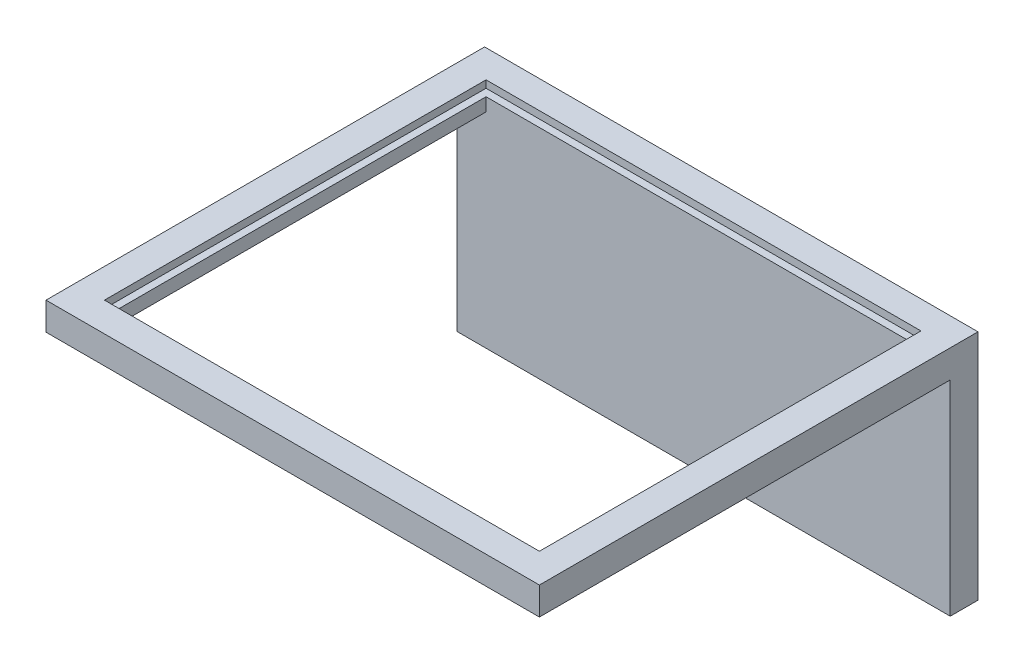
SolidWorks part; units mm, degrees
ref_plane "Plan de face" through (0, 0, 0) normal (0, 0, 1) x (1, 0, 0)
ref_plane "Plan de dessus" through (0, 0, 0) normal (0, 1, 0) x (1, 0, 0)
ref_plane "Plan de droite" through (0, 0, 0) normal (1, 0, 0) x (0, 0, -1)
sketch "Esquisse1" plane through (0, 0, 0) normal (0, 0, 1) x (1, 0, 0)
  line L1 (0, 0) -> (33.75, 0)
  line L2 (0, 0) -> (0, 14)
  line L3 (0, 14) -> (33.75, 14)
  line L4 (33.75, 0) -> (33.75, 14)
  point P4 (0, 0)
  dimension "D1" = 33.75
  dimension "D2" = 14
extrude "Boss.-Extru.1" add sketch "Esquisse1" along normal blind 1.9
sketch "Esquisse2" plane through (0, 14, 0) normal (0, 1, 0) x (1, 0, 0)
  line L0 (33.75, -1.9) -> (33.75, 0) construction
  line L1 (0, 0) -> (33.75, 0)
  line L2 (0, 0) -> (0, -30)
  line L3 (0, -30) -> (33.75, -30)
  line L4 (33.75, 0) -> (33.75, -30)
  line L5 (33.75, -1.9) -> (0, -1.9) construction
  line L6 (2, -1.9) -> (31.75, -1.9)
  line L7 (2, -1.9) -> (2, -28)
  line L8 (2, -28) -> (31.75, -28)
  line L9 (31.75, -1.9) -> (31.75, -28)
  point P11 (0, 0)
  point P12 (0, 0)
  point P13 (2, -1.9)
  line M9 (33.75, 0) -> (0, 0)
  line M10 (0, 0) -> (0, -1.9)
  line M11 (0, -1.9) -> (33.75, -1.9)
  line M12 (33.75, -1.9) -> (33.75, 0)
  dimension "D1" = 30
  dimension "D2" = 2
  dimension "D3" = 2
  dimension "D4" = 2
extrude "Boss.-Extru.2" add sketch "Esquisse2" along normal blind 1.9 contours L9 L8 L7 L2 L3 L4 M11 | L7 M9 M10 M11 | L9 M9 M11 M12
sketch "Esquisse4" plane through (0, 15.9, 0) normal (0, 1, 0) x (1, 0, 0)
  line L0 (2, -1.9) -> (0, -1.9) construction
  line L7 (33.75, 0) -> (0, 0) construction
  line L9 (1, 0) -> (32.75, 0)
  line L10 (1, 0) -> (1, -29)
  line L11 (1, -29) -> (32.75, -29)
  line L12 (32.75, 0) -> (32.75, -29)
  line L13 (31.75, -1.9) -> (33.75, -1.9) construction
  line L14 (33.75, 0) -> (33.75, -30) construction
  line L15 (31.75, -28) -> (31.75, -30) construction
  line L16 (0, -30) -> (33.75, -30) construction
  point P14 (32.75, -1.9)
  point P19 (1, -1.9)
  point P25 (31.75, -29)
extrude "Enlèv. mat.-Extru.1" cut sketch "Esquisse4" against normal blind 0.5 from offset 0.5 offset against normal yes
chamfer "Chanfrein1" distance 0.3 angle 45 6 edges at (32.75, 15.15, 0) (16.875, 15.4, 0) (1, 15.15, 0) (16.875, 14.9, 0) (16.875, 14.9, 28) (16.875, 15.4, 28)
